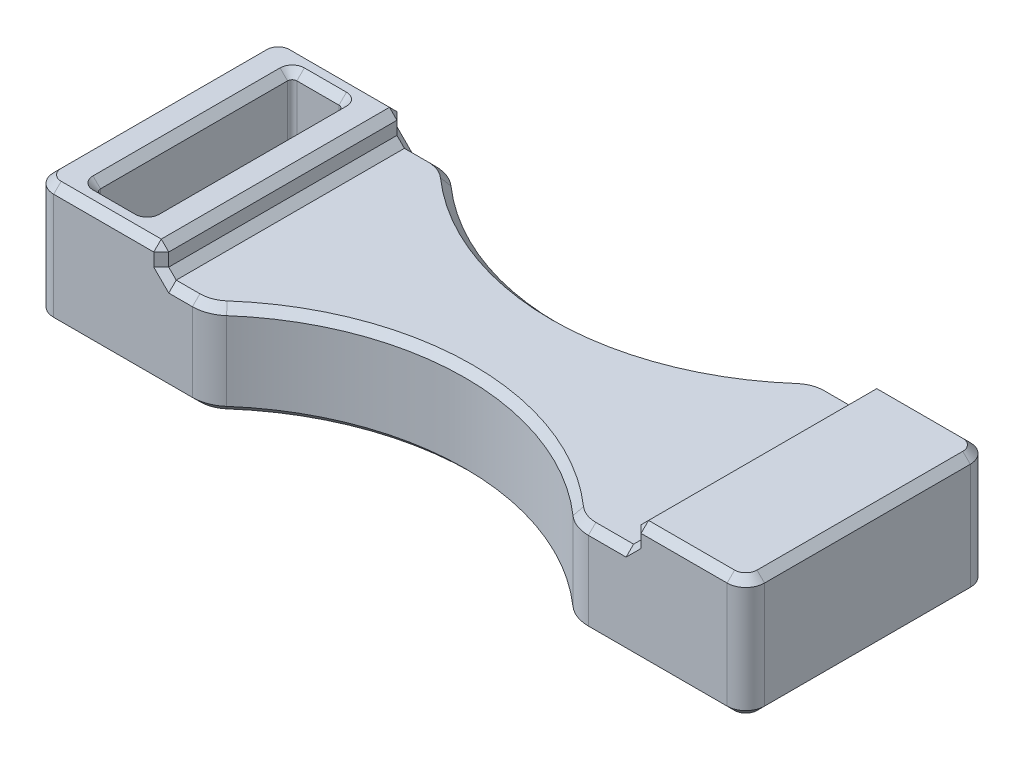
SolidWorks part; units mm, degrees
ref_plane "Front Plane" through (0, 0, 0) normal (0, 0, 1) x (1, 0, 0)
ref_plane "Top Plane" through (0, 0, 0) normal (0, 1, 0) x (1, 0, 0)
ref_plane "Right Plane" through (0, 0, 0) normal (1, 0, 0) x (0, 0, -1)
sketch "Sketch1" plane through (0, 0, 0) normal (0, 1, 0) x (1, 0, 0)
  line L1 (18, 6.5) -> (9.798, 6.5)
  line L2 (19, 5.5) -> (19, -5.5)
  line L3 (18, -6.5) -> (9.798, -6.5)
  line L5 (19, 6.5) -> (-18.1113, -6.196) construction
  line L6 (19, -6.5) -> (-17.5, 5.9868) construction
  line L7 (-16.75, -5.25) -> (-14.5, -5.25)
  line L12 (-14.25, -5) -> (-14.25, 5)
  line L13 (-14.5, 5.25) -> (-16.75, 5.25)
  line L14 (-19, -5.5) -> (-19, 5.5)
  line L15 (-17, -5) -> (-17, 5)
  line L16 (-9.798, 6.5) -> (-18, 6.5)
  line L17 (-9.798, -6.5) -> (-18, -6.5)
  arc A0 (18, 6.5) -> (19, 5.5) centre (18, 5.5) cw
  arc A1 (19, -5.5) -> (18, -6.5) centre (18, -5.5) cw
  arc A6 (-14.5, -5.25) -> (-14.25, -5) centre (-14.5, -5) ccw
  arc A7 (-14.25, 5) -> (-14.5, 5.25) centre (-14.5, 5) ccw
  arc A10 (-16.75, -5.25) -> (-17, -5) centre (-16.75, -5) cw
  arc A11 (-16.75, 5.25) -> (-17, 5) centre (-16.75, 5) ccw
  arc A12 (-19, 5.5) -> (-18, 6.5) centre (-18, 5.5) cw
  arc A13 (-19, -5.5) -> (-18, -6.5) centre (-18, -5.5) ccw
  arc A14 (-9.798, 6.5) -> (9.798, 6.5) centre (0, 16.5) ccw
  arc A15 (-9.798, -6.5) -> (9.798, -6.5) centre (0, -16.5) cw
  point P0 (0, 0)
  point P12 (-14.25, 0)
  point P22 (-18, -5.25)
  point P28 (-17, 0)
  point P29 (19, 0)
  point P45 (0, 2.5)
  point P50 (0, -2.5)
  dimension "D3" = 1
  dimension "D6" = 0.25
  dimension "D7" = 0.25
  dimension "D10" = 1
  dimension "D11" = 14
  dimension "D1" = 36
  dimension "D2" = 13
  dimension "D4" = 10.5
  dimension "D5" = 2.75
  dimension "D8" = 1.5
  dimension "D9" = 38
  dimension "D12" = 2.5
extrude "Boss-Extrude1" add sketch "Sketch1" along normal mid plane 6.5
sketch "Sketch2" plane through (0, 3.25, 0) normal (0, 1, 0) x (1, 0, 0)
  line L0 (13, 6.5) -> (13, -6.5)
  line L1 (13, -6.5) -> (-12.25, -6.5)
  line L2 (-12.25, -6.5) -> (-12.25, 6.5)
  line L3 (-12.25, 6.5) -> (13, 6.5)
  line L4 (19, -5.5) -> (19, 5.5) construction
  line L5 (-14.25, 5) -> (-14.25, -5) construction
  line L6 (18, 6.5) -> (9.798, 6.5) construction
  line L7 (9.798, -6.5) -> (18, -6.5) construction
  dimension "D1" = 6
  dimension "D2" = 2
extrude "Cut-Extrude1" cut sketch "Sketch2" against normal blind 1.5
fillet "Fillet1" radius 2 4 edges at (-9.798, -0.75, -6.5) (9.798, -0.75, -6.5) (9.798, -0.75, 6.5) (-9.798, -0.75, 6.5)
chamfer "Chamfer1" distance 0.4 angle 45 60 edges at (-16.9268, -3.25, -5.1768) (-15.625, -3.25, -5.25) (-14.3232, -3.25, -5.1768) (-14.25, -3.25, 0) (-14.3232, -3.25, 5.1768) (-15.625, -3.25, 5.25) (-16.9268, -3.25, 5.1768) (-17, -3.25, 0) (-18.7071, -3.25, -6.2071) (-19, -3.25, 0) (-18.7071, -3.25, 6.2071) (-14.2915, -3.25, 6.5) (-9.8759, -3.25, 6.3708) (0, -3.25, 2.5) (9.8759, -3.25, 6.3708) (14.2915, -3.25, 6.5) (18.7071, -3.25, 6.2071) (19, -3.25, 0) (18.7071, -3.25, -6.2071) (14.2915, -3.25, -6.5) (9.8759, -3.25, -6.3708) (0, -3.25, -2.5) (-9.8759, -3.25, -6.3708) (-14.2915, -3.25, -6.5) (18.7071, 3.25, -6.2071) (19, 3.25, 0) (18.7071, 3.25, 6.2071) (15.5, 3.25, 6.5) (13, 3.25, 0) (15.5, 3.25, -6.5) (-15.625, 3.25, 5.25) (-14.3232, 3.25, 5.1768) (-14.25, 3.25, 0) (-14.3232, 3.25, -5.1768) (-15.625, 3.25, -5.25) (-16.9268, 3.25, -5.1768) (-17, 3.25, 0) (-16.9268, 3.25, 5.1768) (-18.7071, 3.25, 6.2071) (-19, 3.25, 0) (-18.7071, 3.25, -6.2071) (-15.125, 3.25, -6.5) (-12.25, 3.25, 0) (-15.125, 3.25, 6.5) (13, 2.5, -6.5) (13, 2.5, 6.5) (-12.25, 2.5, 6.5) (-12.25, 2.5, -6.5) (9.8759, 1.75, -6.3708) (11.7915, 1.75, -6.5) (13, 1.75, 0) (11.7915, 1.75, 6.5) (9.8759, 1.75, 6.3708) (0, 1.75, 2.5) (-9.8759, 1.75, 6.3708) (-11.4165, 1.75, 6.5) (-12.25, 1.75, 0) (-11.4165, 1.75, -6.5) (-9.8759, 1.75, -6.3708) (0, 1.75, -2.5)
